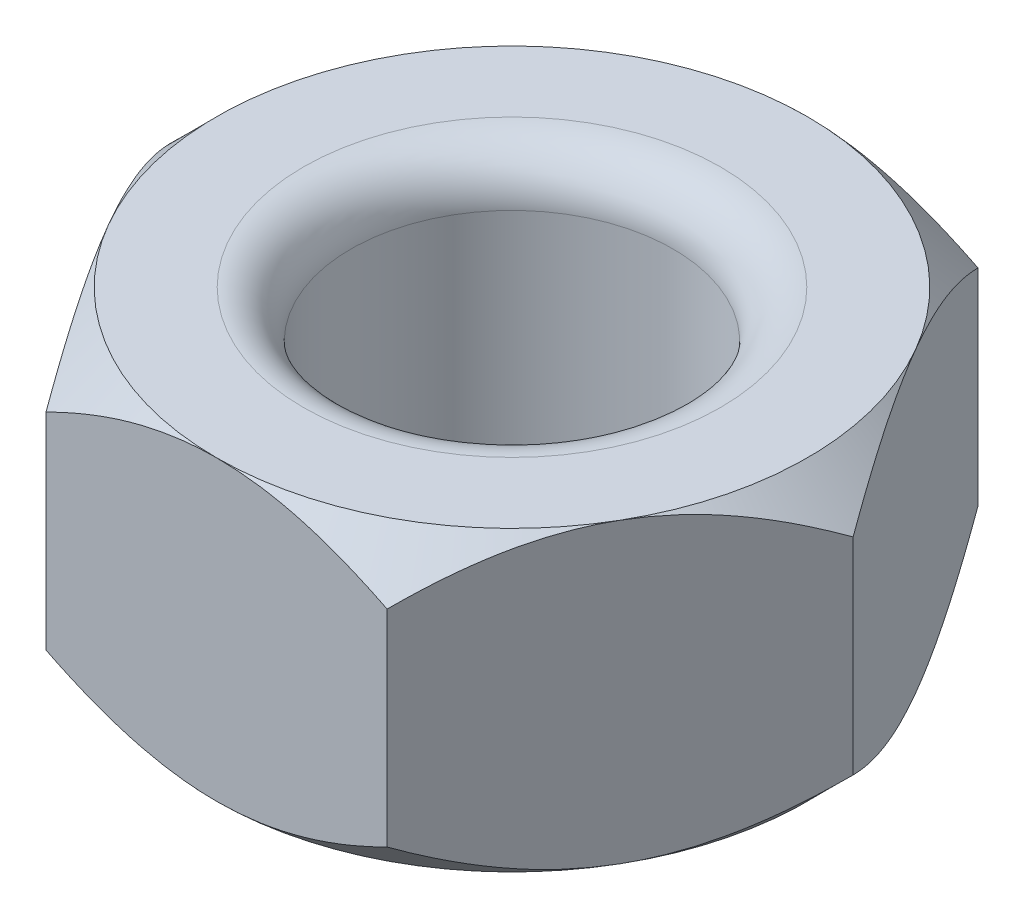
SolidWorks part; units mm, degrees
ref_plane "Спереди" through (0, 0, 0) normal (0, 0, 1) x (1, 0, 0)
ref_plane "Сверху" through (0, 0, 0) normal (0, 1, 0) x (1, 0, 0)
ref_plane "Справа" through (0, 0, 0) normal (1, 0, 0) x (0, 0, -1)
sketch "Эскиз1" plane through (0, 0, 0) normal (0, 1, 0) x (1, 0, 0)
  line L1 (7.2, 0) -> (3.6, 6.2354)
  line L2 (3.6, 6.2354) -> (-3.6, 6.2354)
  line L3 (-3.6, 6.2354) -> (-7.2, 0)
  line L4 (-7.2, 0) -> (-3.6, -6.2354)
  line L5 (-3.6, -6.2354) -> (3.6, -6.2354)
  line L6 (3.6, -6.2354) -> (7.2, 0)
  circle A0 centre (0, 0) radius 6.2354 construction
  dimension "D1" = 14.4
extrude "Бобышка-Вытянуть1" add sketch "Эскиз1" along normal blind 6.28
sketch "Эскиз2" plane through (0, 6.28, 0) normal (0, 1, 0) x (1, 0, 0)
  line L0 (-3.6, 6.2354) -> (-7.2, 0) construction
  circle A0 centre (0, 0) radius 6.2354
extrude "Вырез-Вытянуть2" cut sketch "Эскиз2" against normal blind 1 draft 45 flip side to cut contours A0
sketch "Эскиз3" plane through (0, 0, 0) normal (0, -1, 0) x (1, 0, 0)
  circle A0 centre (0, 0) radius 6.2354
extrude "Вырез-Вытянуть3" cut sketch "Эскиз3" against normal blind 1 draft 45 flip side to cut
sketch "Эскиз4" plane through (0, 6.28, 0) normal (0, 1, 0) x (1, 0, 0)
  circle A0 centre (0, 0) radius 3.4
  dimension "D1" = 6.8
extrude "Вырез-Вытянуть4" cut sketch "Эскиз4" against normal through all contours A0
fillet "Скругление1" radius 1 1 edges at (0, 6.28, 3.4)
fillet "Скругление2" radius 1 1 edges at (0, 0, 3.4)
